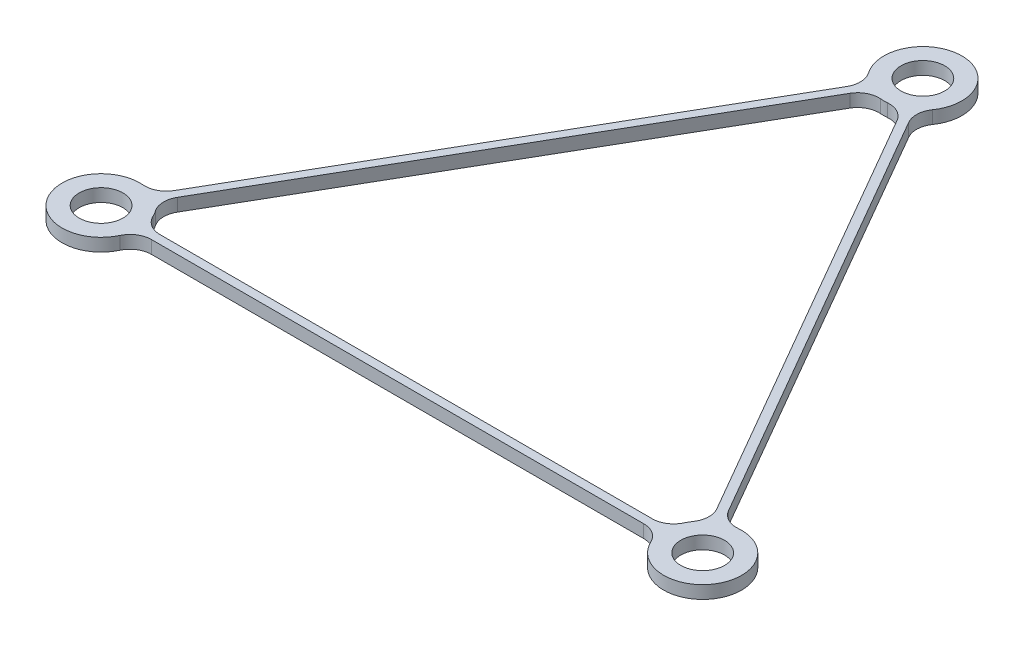
SolidWorks part; units mm, degrees
other "Markup1"
sketch "Sketch1" plane through (0, 0, 0) normal (0.4, 0.515, 0.7581) x (0.8844, 0, -0.4667)
ref_plane "Front Plane" through (0, 0, 0) normal (0, 0, 1) x (1, 0, 0)
ref_plane "Top Plane" through (0, 0, 0) normal (0, 1, 0) x (1, 0, 0)
ref_plane "Right Plane" through (0, 0, 0) normal (1, 0, 0) x (0, 0, -1)
sketch "Sketch2" plane through (0, 0, 0) normal (0, 1, 0) x (1, 0, 0)
  line L0 (35.1, -20.265) -> (0, 0) construction
  line L1 (0, 0) -> (0, 40.53) construction
  line L2 (0, 0) -> (-35.1, -20.265) construction
  line L3 (35.1, -20.265) -> (-35.1, -20.265) construction
  line L4 (-35.1, -20.265) -> (0, 40.53) construction
  line L5 (0, 40.53) -> (35.1, -20.265) construction
  line L6 (-33.2718, -16.0984) -> (-2.6942, 36.8634)
  line L7 (33.2718, -16.0984) -> (2.6942, 36.8634)
  line L8 (30.5776, -20.765) -> (-30.5776, -20.765)
  line L9 (-30.5776, -19.765) -> (30.5776, -19.765)
  line L10 (32.4058, -16.5984) -> (1.8282, 36.3634)
  line L11 (-1.8282, 36.3634) -> (-32.4058, -16.5984)
  line L12 (-17.983, 10.3825) -> (-17.117, 9.8825) construction
  line L13 (0, -20.765) -> (0, -19.765) construction
  line L14 (17.983, 10.3825) -> (17.117, 9.8825) construction
  circle A0 centre (0, 40.53) radius 2.55
  circle A1 centre (35.1, -20.265) radius 2.55
  circle A2 centre (-35.1, -20.265) radius 2.55
  arc A3 (32.4058, -16.5984) -> (30.5776, -19.765) centre (35.1, -20.265) ccw
  arc A4 (-30.5776, -19.765) -> (-32.4058, -16.5984) centre (-35.1, -20.265) ccw
  arc A5 (2.6942, 36.8634) -> (-2.6942, 36.8634) centre (0, 40.53) ccw
  arc A6 (30.5776, -20.765) -> (33.2718, -16.0984) centre (35.1, -20.265) ccw
  arc A7 (-33.2718, -16.0984) -> (-30.5776, -20.765) centre (-35.1, -20.265) ccw
  arc A8 (-1.8282, 36.3634) -> (1.8282, 36.3634) centre (0, 40.53) ccw
  point P14 (17.55, 10.1325)
  point P21 (-17.55, 10.1325)
  point P23 (0, -20.265)
  dimension "D2" = 5.1
  dimension "D3" = 2
  dimension "D1" = 70.2
  dimension "D4" = 1
extrude "main_shape" add sketch "Sketch2" along normal mid plane 1.5 contours A5 L6 A7 L8 A6 L7
fillet "outside_fillet" radius 2.5 6 edges at (-2.6942, 0, -36.8634) (2.6942, 0, -36.8634) (33.2718, 0, 16.0984) (30.5776, 0, 20.765) (-30.5776, 0, 20.765) (-33.2718, 0, 16.0984)
fillet "inside_fillet" radius 2.5 6 edges at (-32.4058, 0, 16.5984) (-30.5776, 0, 19.765) (30.5776, 0, 19.765) (32.4058, 0, 16.5984) (1.8282, 0, -36.3634) (-1.8282, 0, -36.3634)
